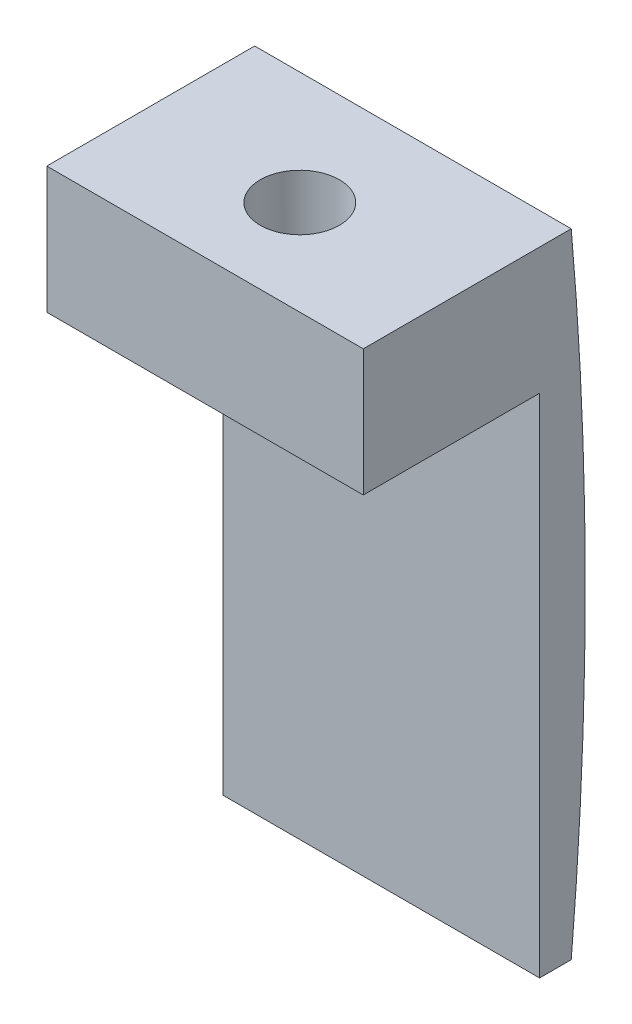
SolidWorks part; units mm, degrees
ref_plane "Front Plane" through (0, 0, 0) normal (0, 0, 1) x (1, 0, 0)
ref_plane "Top Plane" through (0, 0, 0) normal (0, 1, 0) x (1, 0, 0)
ref_plane "Right Plane" through (0, 0, 0) normal (1, 0, 0) x (0, 0, -1)
sketch "Sketch1" plane through (0, 0, 0) normal (1, 0, 0) x (0, 0, -1)
  line L1 (0.3629, 7.2582) -> (-0.2067, 7.2582)
  line L2 (0.3629, 7.2582) -> (0.3629, -12.7418)
  line L3 (0.3629, -12.7418) -> (-0.6371, -12.7418)
  line L4 (-0.6371, 3.2582) -> (-0.6371, -12.7418)
  line L5 (0.3629, 7.2582) -> (-0.6371, -12.7418) construction
  line L6 (0.3629, -12.7418) -> (-0.2067, 7.2582) construction
  line L7 (-0.2067, 7.2582) -> (-6.2067, 7.2582)
  line L9 (-0.6371, 3.2582) -> (-6.2067, 3.2582)
  line L10 (-6.2067, 7.2582) -> (-6.2067, 3.2582)
  point P0 (0, 0)
  dimension "D1" = 20
  dimension "D2" = 1
  dimension "D3" = 4
  dimension "D4" = 6
extrude "Boss-Extrude1" add sketch "Sketch1" along normal blind 10
sketch "Sketch2" plane through (0, 3.2582, 0) normal (0, 1, 0) x (1, 0, 0)
  line L0 (4.9892, -6.1998) -> (5, -0.6371) construction
  line L3 (10, -0.6371) -> (0, -0.6371) construction
  line L4 (10, -6.2067) -> (0, -6.2067) construction
  circle A0 centre (4.995, -3.2067) radius 1.25
  dimension "D1" = 2.5
  dimension "D2" = 3
extrude "Cut-Extrude1" cut sketch "Sketch2" along normal up to surface (4 mm away) up to face at (5, 7.2582, 2.9219)
sketch "Sketch5" plane through (0, 0, 0) normal (-1, 0, 0) x (0, 0, 1)
  line L0 (-0.3629, -12.7418) -> (-0.3629, 7.2582) construction
  line L1 (-0.3629, -12.7418) -> (-0.3629, 7.2582)
  arc A0 (-0.3629, 7.2582) -> (-0.3629, -12.7418) centre (112.4061, -2.7418) ccw
extrude "Boss-Extrude4" add sketch "Sketch5" against normal up to surface (10 mm away) up to face at (10, -0.7418, 2.1603)
